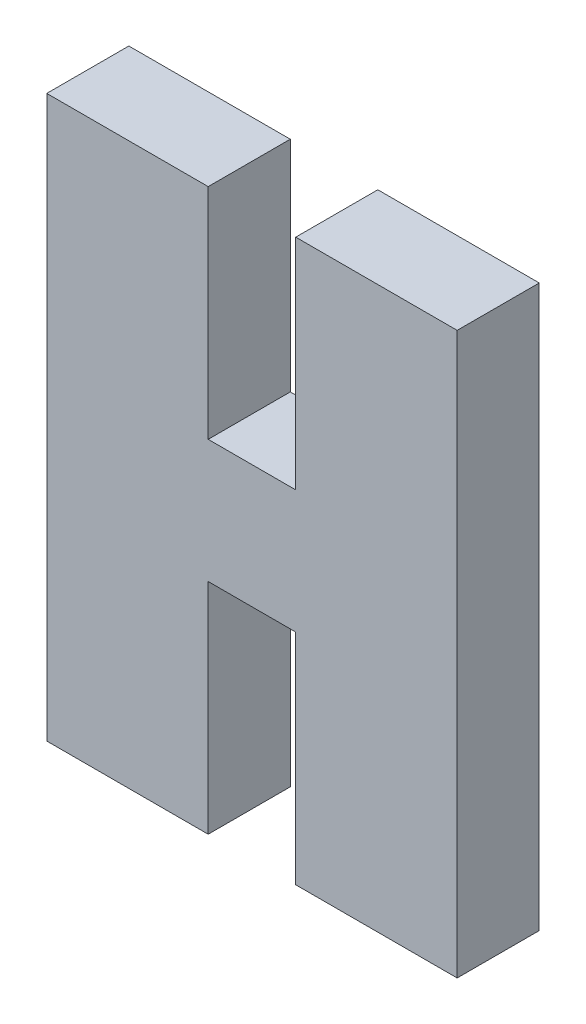
SolidWorks part; units mm, degrees
ref_plane "Alzado" through (0, 0, 0) normal (0, 0, 1) x (1, 0, 0)
ref_plane "Planta" through (0, 0, 0) normal (0, 1, 0) x (1, 0, 0)
ref_plane "Vista lateral" through (0, 0, 0) normal (1, 0, 0) x (0, 0, -1)
sketch "Croquis1" plane through (0, 0, 0) normal (0, 0, 1) x (1, 0, 0)
  line L0 (0, 0) -> (-10.4741, 0) construction
  line L1 (-7.5, 2.25) -> (7.5, 2.25)
  line L2 (-7.5, 2.25) -> (-7.5, -2.25)
  line L3 (-7.5, -2.25) -> (7.5, -2.25)
  line L4 (7.5, 2.25) -> (7.5, -2.25)
  line L5 (-7.5, 2.25) -> (7.5, -2.25) construction
  line L6 (-7.5, -2.25) -> (7.5, 2.25) construction
  line L7 (0, 0) -> (0, -5.4741) construction
  line L8 (-7.5, 2.25) -> (-1.6, 2.25)
  line L9 (-7.5, 2.25) -> (-7.5, 10.25)
  line L10 (-7.5, 10.25) -> (-1.6, 10.25)
  line L11 (-1.6, 2.25) -> (-1.6, 10.25)
  line L12 (7.5, 10.25) -> (1.6, 10.25)
  line L13 (1.6, 2.25) -> (1.6, 10.25)
  line L14 (7.5, 2.25) -> (1.6, 2.25)
  line L15 (7.5, 2.25) -> (7.5, 10.25)
  line L16 (7.5, -2.25) -> (1.6, -2.25)
  line L17 (1.6, -2.25) -> (1.6, -10.25)
  line L18 (7.5, -10.25) -> (1.6, -10.25)
  line L19 (7.5, -2.25) -> (7.5, -10.25)
  line L20 (-7.5, -10.25) -> (-1.6, -10.25)
  line L21 (-1.6, -2.25) -> (-1.6, -10.25)
  line L22 (-7.5, -2.25) -> (-1.6, -2.25)
  line L23 (-7.5, -2.25) -> (-7.5, -10.25)
  point P0 (0, 0)
  dimension "D1" = 4.5
  dimension "D2" = 15
  dimension "D3" = 3.2
  dimension "D4" = 8
extrude "Saliente-Extruir1" add sketch "Croquis1" along normal blind 3 contours L1 L11 L10 L9 | L1 L15 L12 L13 | L4 L1 L2 L3 | L19 L3 L17 L18 | L3 L23 L20 L21
